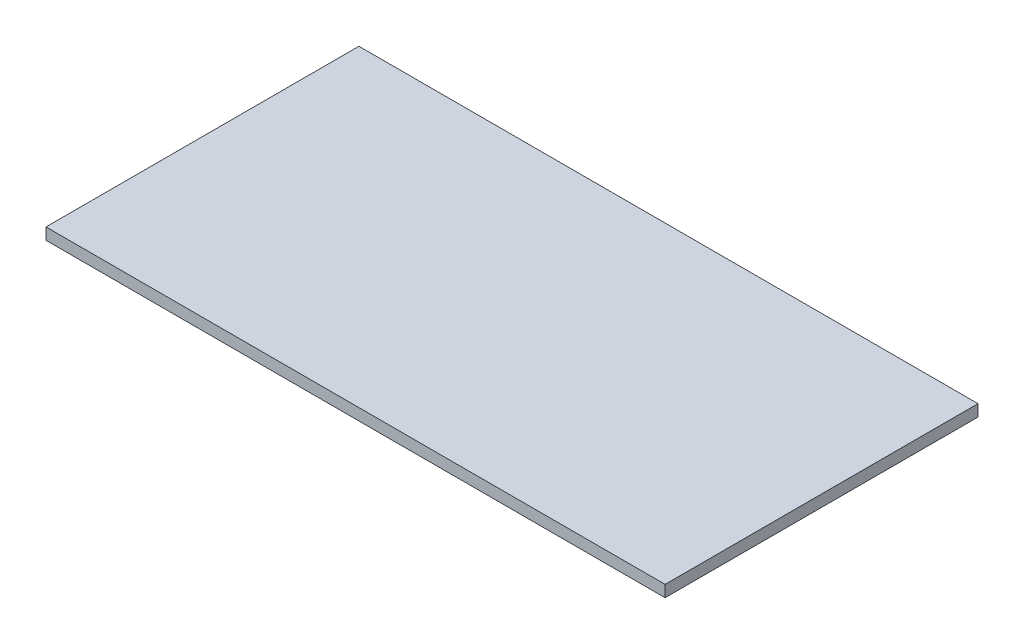
SolidWorks part; units mm, degrees
ref_plane "Front Plane" through (0, 0, 0) normal (0, 0, 1) x (1, 0, 0)
ref_plane "Top Plane" through (0, 0, 0) normal (0, 1, 0) x (1, 0, 0)
ref_plane "Right Plane" through (0, 0, 0) normal (1, 0, 0) x (0, 0, -1)
sketch "Sketch1" plane through (0, 0, 0) normal (0, 1, 0) x (1, 0, 0)
  line L1 (0, 0) -> (-162.56, 0)
  line L2 (0, 0) -> (0, 82.169)
  line L3 (0, 82.169) -> (-162.56, 82.169)
  line L4 (-162.56, 0) -> (-162.56, 82.169)
  dimension "D1" = 162.56
  dimension "D2" = 82.169
extrude "Boss-Extrude1" add sketch "Sketch1" along normal blind 3.048
